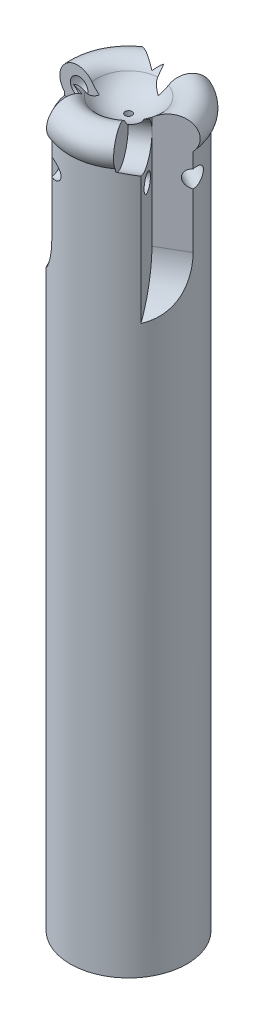
SolidWorks part; units mm, degrees
ref_plane "前视基准面" through (0, 0, 0) normal (0, 0, 1) x (1, 0, 0)
ref_plane "上视基准面" through (0, 0, 0) normal (0, 1, 0) x (1, 0, 0)
ref_plane "右视基准面" through (0, 0, 0) normal (1, 0, 0) x (0, 0, -1)
sketch "草图1" plane through (0, 0, 0) normal (0, 0, 1) x (1, 0, 0)
  line L0 (0, 98.0078) -> (0, -87.4292) construction
  line L1 (-10, 64.6639) -> (-10, -55.3361)
  line L2 (-0.3278, 65.9104) -> (0, 65.9104)
  line L3 (0, 65.9104) -> (0, -55.3361)
  line L4 (0, -55.3361) -> (-10, -55.3361)
  arc A0 (-10, 64.6639) -> (-10.825, 66.7302) centre (-7.825, 66.7302) cw
  arc A1 (-10.825, 66.7302) -> (-5.3714, 68.4564) centre (-7.825, 66.7302) cw
  arc A2 (-5.3714, 68.4564) -> (-0.3278, 65.9104) centre (-0.4642, 71.9088) ccw
  dimension "D2" = 3
  dimension "D3" = 3
  dimension "D4" = 6
  dimension "D1" = 10
  dimension "D5" = 120
revolve "旋转1" add sketch "草图1" angle 360 about L0
ref_plane "基准面1" through (0, 0, 24) normal (0, 0, 1) x (1, 0, 0)
sketch "草图3" plane through (0, 0, 24) normal (0, 0, 1) x (1, 0, 0)
  line L0 (-4, 69.7302) -> (-12.715, 69.7302)
  line L1 (-12.715, 69.7302) -> (-12.715, 41.4057)
  line L2 (-12.715, 41.4057) -> (-10, 41.4057)
  line L5 (-4, 49.687) -> (-4, 69.7302)
  line L10 (7.825, 69.7302) -> (-7.825, 69.7302) construction
  arc A15 (-4, 49.687) -> (-10, 41.4057) centre (-12.715, 49.687) cw
extrude "切除-拉伸1" cut sketch "草图3" against normal blind 20
sketch "草图6" plane through (0, 0, 4) normal (0, 0, 1) x (1, 0, 0)
  line L0 (-9.1652, 64.6639) -> (-9.1652, 41.7277) construction
  circle A0 centre (-7.4652, 66.6639) radius 3.5
  dimension "D1" = 7
  dimension "D3" = 2
  dimension "D2" = 1.7
extrude "切除-拉伸2" cut sketch "草图6" against normal blind 3
sketch "草图8" plane through (0, 0, 4) normal (0, 0, 1) x (1, 0, 0)
  line L1 (-9.1652, 63.6045) -> (-9.1652, 41.7277) construction
  circle A0 centre (-6.1652, 60.6045) radius 1.5
  dimension "D1" = 3
  dimension "D2" = 3
  dimension "D3" = 3
extrude "切除-拉伸3" cut sketch "草图8" against normal through all
cosmetic thread "装饰螺纹线2" parameters "D2"=9
sketch "草图10" plane through (0, 65.9104, 0) normal (0, 1, 0) x (1, 0, 0)
  circle A0 centre (0, 0) radius 1.5
  dimension "D1" = 3
extrude "切除-拉伸5" cut sketch "草图10" against normal blind 2
sketch "草图12" plane through (0, 0, 1) normal (0, 0, 1) x (1, 0, 0)
  circle A0 centre (-7.4652, 66.6639) radius 1.5
  dimension "D1" = 3
extrude "切除-拉伸6" cut sketch "草图12" against normal through all
cosmetic thread "装饰螺纹线1" parameters "D2"=9
pattern_circular "阵列(圆周)1" count 3 over 360 about axis through (0, 0, 0) along (0, 1, 0) of "切除-拉伸1", "切除-拉伸2", "切除-拉伸3"
